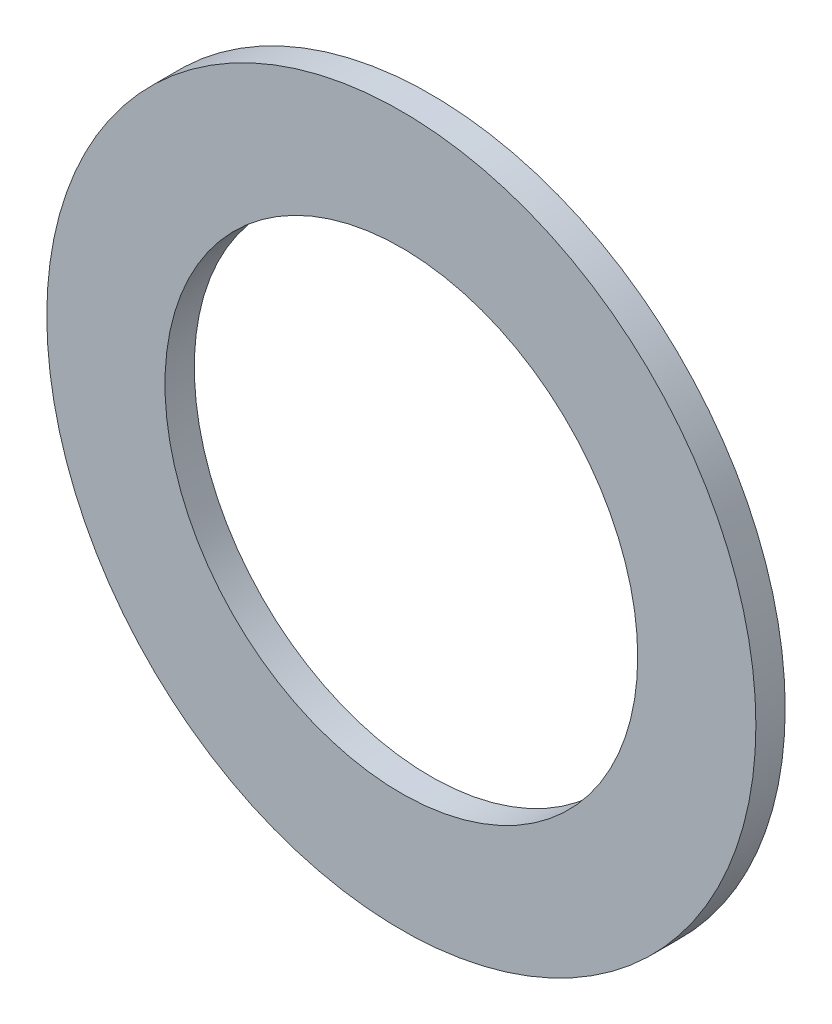
SolidWorks part; units mm, degrees
material "Plain Carbon Steel"
ref_plane "Front Plane" through (0, 0, 0) normal (0, 0, 1) x (1, 0, 0)
ref_plane "Top Plane" through (0, 0, 0) normal (0, 1, 0) x (1, 0, 0)
ref_plane "Right Plane" through (0, 0, 0) normal (1, 0, 0) x (0, 0, -1)
sketch "Sketch1" plane through (0, 0, 0) normal (0, 0, 1) x (1, 0, 0)
  circle A0 centre (0, 0) radius 6.35
  circle A1 centre (0, 0) radius 9.525
  dimension "D1" = 19.05
  dimension "D2" = 12.7
extrude "Boss-Extrude1" add sketch "Sketch1" along normal blind 0.7874
